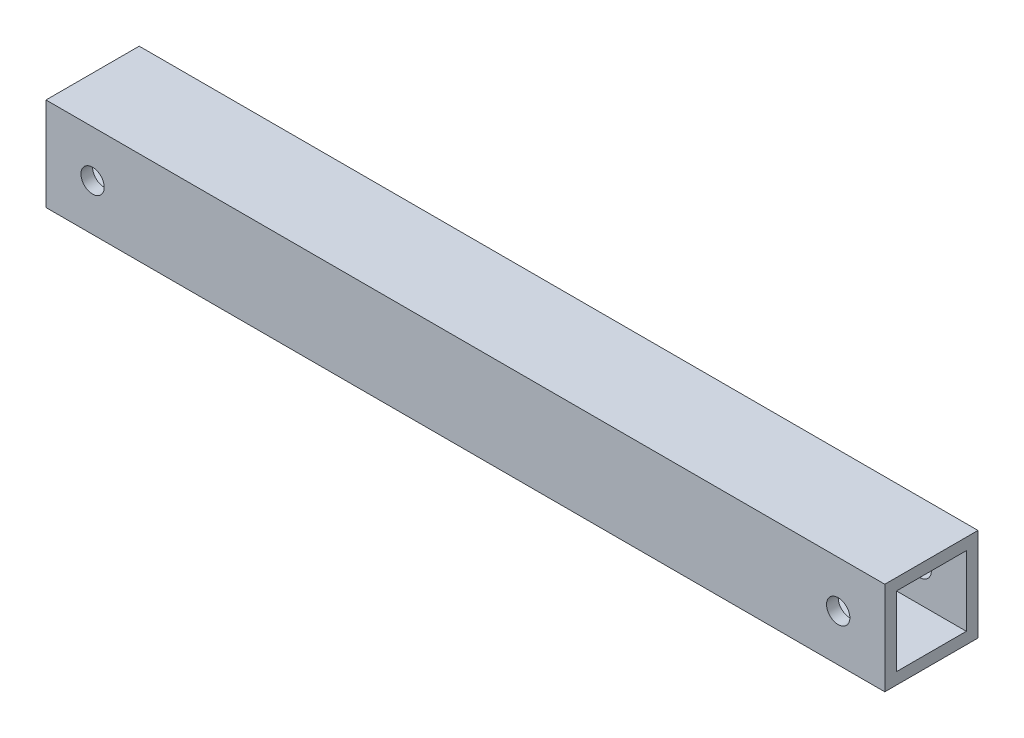
SolidWorks part; units mm, degrees
ref_plane "Front Plane" through (0, 0, 0) normal (0, 0, 1) x (1, 0, 0)
ref_plane "Top Plane" through (0, 0, 0) normal (0, 1, 0) x (1, 0, 0)
ref_plane "Right Plane" through (0, 0, 0) normal (1, 0, 0) x (0, 0, -1)
sketch "Sketch1" plane through (0, 0, 0) normal (0, 0, 1) x (1, 0, 0)
  line L1 (-114.3, -12.7) -> (114.3, -12.7)
  line L2 (-114.3, -12.7) -> (-114.3, 12.7)
  line L3 (-114.3, 12.7) -> (114.3, 12.7)
  line L4 (114.3, -12.7) -> (114.3, 12.7)
  line L5 (-114.3, -12.7) -> (114.3, 12.7) construction
  line L6 (-114.3, 12.7) -> (114.3, -12.7) construction
  point P0 (0, 0)
extrude "Boss-Extrude1" add sketch "Sketch1" along normal blind 25.4
sketch "Sketch2" plane through (114.3, 0, 0) normal (1, 0, 0) x (0, 0, -1)
  line L0 (-12.7, 12.7) -> (-12.7, -12.7)
  line L1 (-25.4, 12.7) -> (0, 12.7) construction
  line L2 (-25.4, -12.7) -> (0, -12.7) construction
  line L3 (-3.175, 9.5204) -> (-3.175, 12.7)
  line L4 (-22.225, -9.5204) -> (-3.175, -9.5204)
  line L5 (-22.225, -9.5204) -> (-22.225, 9.5204)
  line L6 (-22.225, 9.5204) -> (-3.175, 9.5204)
  line L7 (-3.175, -9.5204) -> (-3.175, 9.5204)
  line L8 (-22.225, -9.5204) -> (-3.175, 9.5204) construction
  line L9 (-22.225, 9.5204) -> (-3.175, -9.5204) construction
  line L10 (-3.175, 9.5204) -> (0, 9.5204)
  line L11 (0, -12.7) -> (0, 12.7) construction
  point P6 (-12.7, 0)
extrude "Cut-Extrude1" cut sketch "Sketch2" against normal blind 508 contours L6 L5 L4 L0 | L4 L7 L6 L0
sketch "Sketch4" plane through (0, 0, 25.4) normal (0, 0, 1) x (1, 0, 0)
  line L0 (-114.3, 0) -> (-101.6, 0)
  line L1 (-114.3, 12.7) -> (-114.3, -12.7) construction
  line L2 (114.3, 0) -> (101.6, 0)
  line L4 (114.3, -12.7) -> (114.3, 12.7) construction
  circle A0 centre (-101.6, 0) radius 3.175
  circle A1 centre (101.6, 0) radius 3.175
extrude "Cut-Extrude3" cut sketch "Sketch4" against normal blind 508
